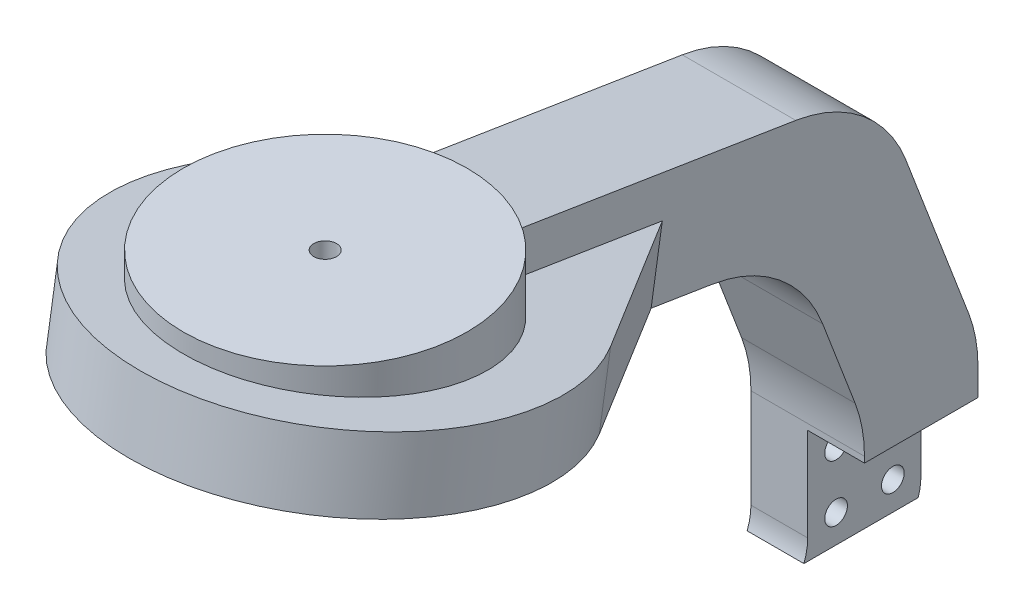
SolidWorks part; units mm, degrees
ref_plane "Alzado" through (0, 0, 0) normal (0, 0, 1) x (1, 0, 0)
ref_plane "Planta" through (0, 0, 0) normal (0, 1, 0) x (1, 0, 0)
ref_plane "Vista lateral" through (0, 0, 0) normal (1, 0, 0) x (0, 0, -1)
sketch "Croquis1" plane through (0, 0, 0) normal (0, 1, 0) x (1, 0, 0)
  circle A0 centre (0, 0) radius 25
  circle A1 centre (0, 0) radius 2
  dimension "D1" = 50
  dimension "D2" = 4
extrude "Saliente-Extruir1" add sketch "Croquis1" along normal blind 20
sketch "Croquis3" plane through (0, 0, 0) normal (1, 0, 0) x (0, 0, -1)
  line L1 (25, 20) -> (-25, 20) construction
  line L2 (0, 20) -> (0, 0) construction
  line L3 (-25, 0) -> (25, 0) construction
  line L5 (0, 20) -> (25, 16)
  line L6 (25, 0) -> (25, 20) construction
  line L7 (0, 0) -> (25, -4)
  line L8 (25, 16) -> (87.1552, 6.0552)
  line L9 (87.1552, 6.0552) -> (105, -40.652)
  line L10 (105, -40.652) -> (105, -70)
  line L11 (25, -4) -> (72.4899, -11.5984)
  line L12 (72.4899, -11.5984) -> (85, -44.3425)
  line L13 (85, -44.3425) -> (85, -70)
  line L14 (85, -70) -> (105, -70)
  line L15 (0, 20) -> (0, 0)
  dimension "D1" = 70
  dimension "D2" = 4
  dimension "D3" = 4
  dimension "D4" = 20
  dimension "D5" = 20
  dimension "D6" = 20
  dimension "D7" = 120
  dimension "D8" = 50
  dimension "D9" = 80
extrude "Saliente-Extruir2" add sketch "Croquis3" along normal mid plane 20
sketch "Croquis4" plane through (0, 0, 0) normal (0, -0.9874, 0.158) x (1, 0, 0)
  line L0 (-10, -22.6251) -> (-10, -73.4119) construction
  line L1 (-10, -73.4119) -> (10, -73.4119) construction
  line L2 (10, -73.4119) -> (10, -48.0185) construction
  line L3 (10, 0) -> (10, -73.4119) construction
  line L4 (-10, -48.0185) -> (-29.0971, -19.4514)
  line L5 (10, -48.0185) -> (29.0971, -19.4514)
  line L6 (-10, -48.0185) -> (10, -48.0185)
  arc A0 (29.0971, -19.4514) -> (-29.0971, -19.4514) centre (0, 0) ccw
  dimension "D1" = 35
extrude "Saliente-Extruir3" add sketch "Croquis4" against normal blind 12.5
sketch "Croquis5" plane through (10, 0, 0) normal (1, 0, 0) x (0, 0, -1)
  line L0 (85, -70) -> (85, -50)
  line L1 (85, -44.3425) -> (85, -70) construction
  line L2 (85, -50) -> (105, -50)
  line L3 (105, -70) -> (105, -40.652) construction
  line L4 (105, -50) -> (105, -70)
  line L5 (105, -70) -> (85, -70)
  dimension "D1" = 20
extrude "Cortar-Extruir1" cut sketch "Croquis5" against normal blind 10
sketch "Croquis6" plane through (0, 0, 0) normal (1, 0, 0) x (0, 0, -1)
  line L0 (85, -70) -> (105, -50) construction
  line L1 (85, -50) -> (105, -70) construction
  circle A0 centre (100, -55) radius 2
  circle A1 centre (100, -65) radius 2
  circle A2 centre (90, -65) radius 2
  circle A3 centre (90, -55) radius 2
  point P16 (95, -60)
  dimension "D1" = 4
  dimension "D2" = 5
extrude "Cortar-Extruir2" cut sketch "Croquis6" against normal blind 10
sketch "Croquis7" plane through (0, 20, 0) normal (0, 1, 0) x (1, 0, 0)
  circle A0 centre (0, 0) radius 2
extrude "Cortar-Extruir3" cut sketch "Croquis7" against normal through all
sketch "Croquis8" plane through (0, 0, 0) normal (0, -1, 0) x (1, 0, 0)
  line L1 (5, 0) -> (2.5, 4.3301)
  line L2 (2.5, 4.3301) -> (-2.5, 4.3301)
  line L3 (-2.5, 4.3301) -> (-5, 0)
  line L4 (-5, 0) -> (-2.5, -4.3301)
  line L5 (-2.5, -4.3301) -> (2.5, -4.3301)
  line L6 (2.5, -4.3301) -> (5, 0)
  circle A0 centre (0, 0) radius 4.3301 construction
  dimension "D1" = 5
extrude "Cortar-Extruir4" cut sketch "Croquis8" against normal mid plane 10
fillet "Redondeo1" radius 25 4 edges at (0, -44.3425, -85) (0, -11.5984, -72.4899) (0, -40.652, -105) (0, 6.0552, -87.1552)
sketch "Croquis9" plane through (-10, 0, 0) normal (-1, 0, 0) x (0, 0, 1)
  line L0 (-85, -70) -> (-84.333, -70)
  line L1 (-85, -70) -> (-85, -66.4149)
  line L2 (-85, -48.9556) -> (-85, -70) construction
  line L3 (-82.961, -66.4149) -> (-85.3764, -66.4149) construction
  arc A0 (-85, -66.4149) -> (-84.333, -70) centre (-75.0321, -66.4149) ccw
extrude "Saliente-Extruir4" add sketch "Croquis9" against normal blind 10
sketch "Croquis10" plane through (0, 0, 0) normal (1, 0, 0) x (0, 0, -1)
  line L0 (105, -66.7546) -> (105, -70)
  line L1 (105, -70) -> (105, -50) construction
  line L2 (105, -70) -> (104.4587, -70)
  line L3 (84.333, -70) -> (105, -70) construction
  line L4 (104.4587, -70) -> (104.7821, -68.8309)
  line L5 (104.7821, -68.8309) -> (105, -66.7546)
  arc A0 (103.0942, -72.6269) -> (105, -66.7546) centre (95, -66.7546) ccw construction
extrude "Cortar-Extruir5" cut sketch "Croquis10" against normal blind 10
